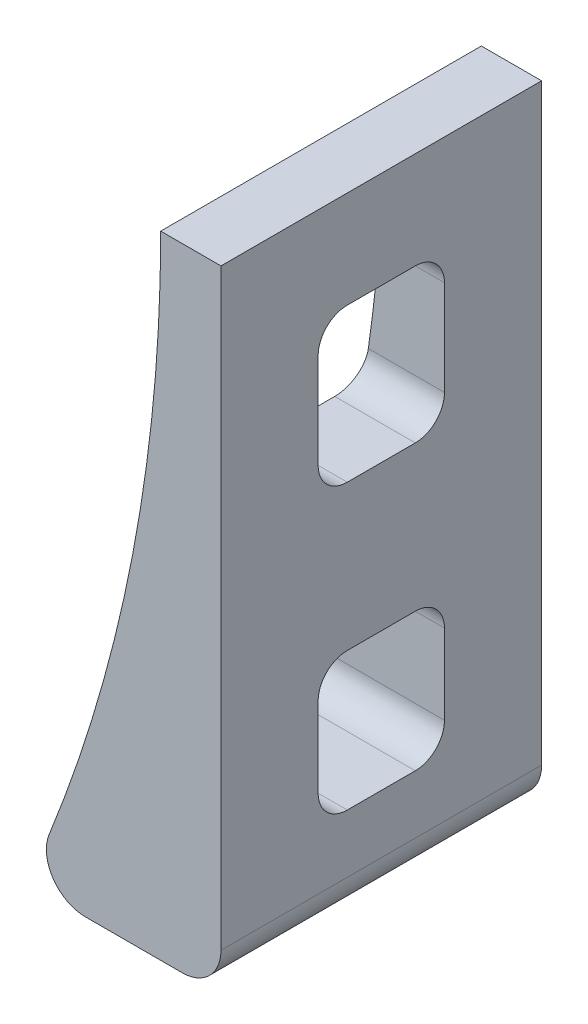
SolidWorks part; units mm, degrees
material "ABS"
ref_plane "Plano frontal" through (0, 0, 0) normal (0, 0, 1) x (1, 0, 0)
ref_plane "Plano superior" through (0, 0, 0) normal (0, 1, 0) x (1, 0, 0)
ref_plane "Plano direito" through (0, 0, 0) normal (1, 0, 0) x (0, 0, -1)
sketch "Esboço1" plane through (0, 0, 0) normal (0, 0, 1) x (1, 0, 0)
  line L0 (-14.0897, 93.1354) -> (-1.0568, 93.1354) construction
  line L1 (-20.2916, 93.1354) -> (-14.0897, 93.1354)
  line L4 (-14.0897, 28.1354) -> (-14.0897, 93.1354)
  line L5 (-34.0897, 28.1354) -> (-14.0897, 28.1354)
  arc A1 (-34.0897, 28.1354) -> (-20.2916, 93.1354) centre (-180.2916, 93.1354) ccw
  dimension "D5" = 160
extrude "Ressalto-extrusão1" add sketch "Esboço1" along normal blind 33
sketch "Esboço2" plane through (-14.0897, 0, 0) normal (1, 0, 0) x (0, 0, -1)
  line L0 (-33, 28.1354) -> (-33, 93.1354) construction
  line L1 (-20, 83.1354) -> (-13, 83.1354)
  line L2 (-23, 80.1354) -> (-23, 70.3568)
  line L3 (-20, 67.3568) -> (-13, 67.3568)
  line L4 (-10, 80.1354) -> (-10, 70.3568)
  line L5 (-20, 52.3568) -> (-13, 52.3568)
  line L6 (-23, 49.3568) -> (-23, 41.1354)
  line L7 (-20, 38.1354) -> (-13, 38.1354)
  line L8 (-10, 49.3568) -> (-10, 41.1354)
  line L9 (0, 28.1354) -> (0, 93.1354) construction
  line L10 (-33, 28.1354) -> (0, 28.1354) construction
  line L11 (-33, 93.1354) -> (0, 93.1354) construction
  arc A0 (-13, 38.1354) -> (-10, 41.1354) centre (-13, 41.1354) ccw
  arc A1 (-23, 41.1354) -> (-20, 38.1354) centre (-20, 41.1354) ccw
  arc A2 (-20, 52.3568) -> (-23, 49.3568) centre (-20, 49.3568) ccw
  arc A3 (-13, 52.3568) -> (-10, 49.3568) centre (-13, 49.3568) cw
  arc A4 (-13, 83.1354) -> (-10, 80.1354) centre (-13, 80.1354) cw
  arc A5 (-13, 67.3568) -> (-10, 70.3568) centre (-13, 70.3568) ccw
  arc A6 (-23, 70.3568) -> (-20, 67.3568) centre (-20, 70.3568) ccw
  arc A7 (-20, 83.1354) -> (-23, 80.1354) centre (-20, 80.1354) ccw
  dimension "D8" = 3
  dimension "D1" = 10
  dimension "D2" = 10
  dimension "D3" = 10
  dimension "D4" = 10
  dimension "D5" = 10
  dimension "D6" = 10
  dimension "D7" = 15
extrude "Corte-extrusão1" cut sketch "Esboço2" against normal blind 33
fillet "Filete1" radius 4 2 edges at (-34.0897, 28.1354, 16.5) (-14.0897, 28.1354, 16.5)
